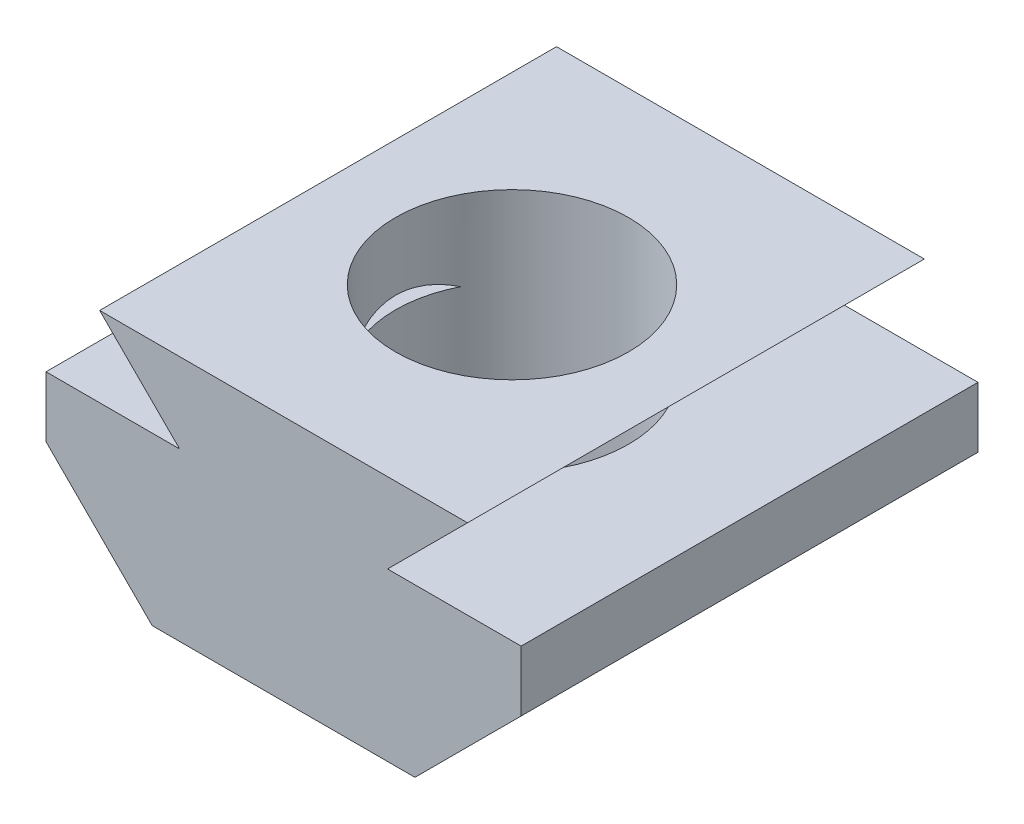
SolidWorks part; units mm, degrees
ref_plane "Alzado" through (0, 0, 0) normal (0, 0, 1) x (1, 0, 0)
ref_plane "Planta" through (0, 0, 0) normal (0, 1, 0) x (1, 0, 0)
ref_plane "Vista lateral" through (0, 0, 0) normal (1, 0, 0) x (0, 0, -1)
sketch "Croquis1" plane through (0, 0, 0) normal (0, 0, 1) x (1, 0, 0)
  line L0 (0, 0) -> (0, -6) construction
  line L1 (0, 0) -> (0, -6) construction
  line L2 (5.5, -3.5) -> (3, -6) construction
  line L3 (5.5, -1.75) -> (5.5, -3.5) construction
  line L4 (3, -1.75) -> (5.5, -1.75) construction
  line L5 (4.75, 0) -> (3, -1.75) construction
  line L6 (-4.75, 0) -> (4.75, 0) construction
  line L7 (-5.5, -3.5) -> (-3, -6) construction
  line L8 (-5.5, -1.75) -> (-5.5, -3.5) construction
  line L9 (-3, -1.75) -> (-5.5, -1.75) construction
  line L10 (-4.75, 0) -> (-3, -1.75) construction
  line L11 (3, -6) -> (-3, -6) construction
  line L12 (-4.0257, -0.3) -> (4.0257, -0.3)
  line L13 (4.0257, -0.3) -> (2.2757, -2.05)
  line L14 (2.2757, -2.05) -> (5.2, -2.05)
  line L15 (5.2, -2.05) -> (5.2, -3.3757)
  line L16 (5.2, -3.3757) -> (2.8757, -5.7)
  line L17 (2.8757, -5.7) -> (-2.8757, -5.7)
  line L18 (-5.2, -3.3757) -> (-2.8757, -5.7)
  line L19 (-5.2, -2.05) -> (-5.2, -3.3757)
  line L20 (-2.2757, -2.05) -> (-5.2, -2.05)
  line L21 (-4.0257, -0.3) -> (-2.2757, -2.05)
  point P12 (0, 0)
  point P13 (2.7042, -6)
  point P14 (0, 0)
  point P16 (0, 0)
  point P17 (0, 0)
  point P18 (0, 0)
  point P19 (4.75, 0)
  point P20 (0, 0)
  point P21 (0, 0)
  point P22 (5.2346, -3.5)
  dimension "D1" = 9.5
  dimension "D2" = 1.75
  dimension "D3" = 1.75
  dimension "D4" = 6
  dimension "D5" = 45
  dimension "D6" = 45
  dimension "D7" = 6
  dimension "D8" = 45
  dimension "D9" = 1.75
  dimension "D10" = 45
  dimension "D11" = 1.75
  dimension "D12" = 0.3
extrude "Saliente-Extruir1" add sketch "Croquis1" along normal blind 10
sketch "Croquis2" plane through (0, -0.3, 0) normal (0, 1, 0) x (1, 0, 0)
  line L0 (-4.0257, 0) -> (4.0257, -10) construction
  circle A0 centre (0, -5) radius 2.55
  point P3 (-1.3203, -5.2378)
  point P5 (0, -5)
  dimension "D1" = 5.1
extrude "Cortar-Extruir1" cut sketch "Croquis2" against normal through all
